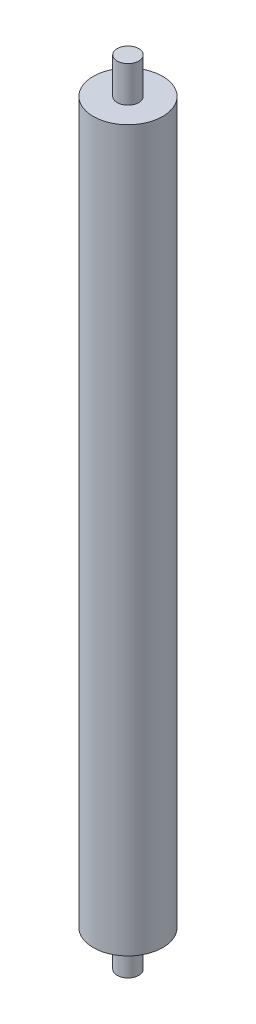
SolidWorks part; units mm, degrees
ref_plane "Front Plane" through (0, 0, 0) normal (0, 0, 1) x (1, 0, 0)
ref_plane "Top Plane" through (0, 0, 0) normal (0, 1, 0) x (1, 0, 0)
ref_plane "Right Plane" through (0, 0, 0) normal (1, 0, 0) x (0, 0, -1)
sketch "Sketch1" plane through (0, 0, 0) normal (0, 1, 0) x (1, 0, 0)
  circle A0 centre (0, 0) radius 24.511
extrude "Boss-Extrude1" add sketch "Sketch1" along normal blind 508
sketch "Sketch2" plane through (0, 0, 0) normal (0, -1, 0) x (1, 0, 0)
  circle A0 centre (0, 0) radius 7.62
extrude "Boss-Extrude2" add sketch "Sketch2" along normal blind 25.4 and the other way blind 533.4
